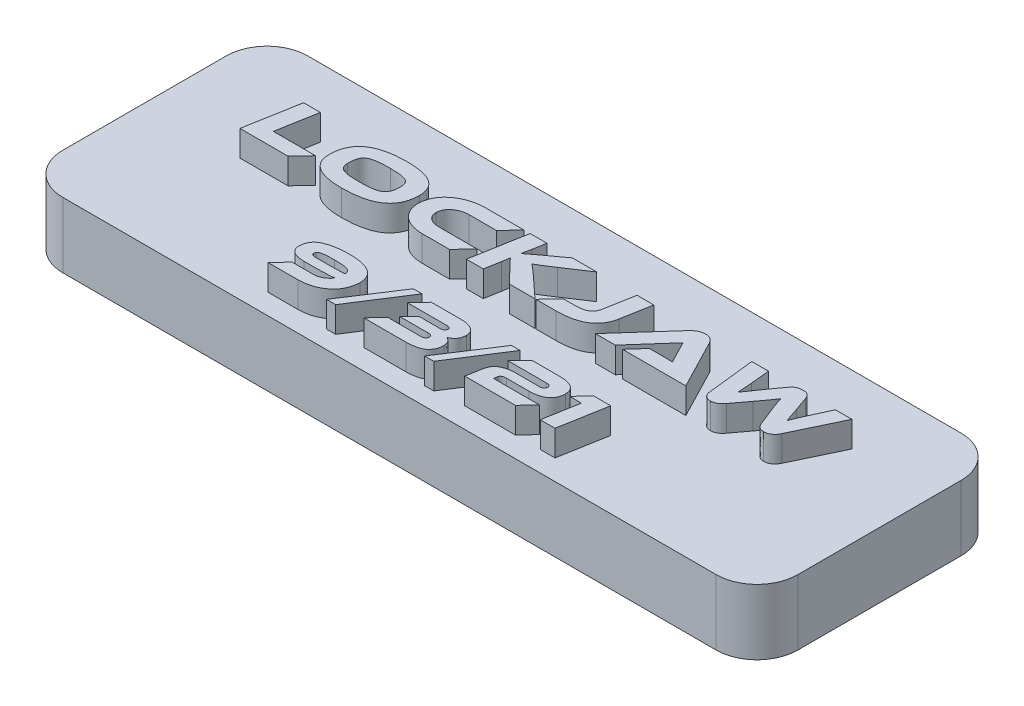
SolidWorks part; units mm, degrees
ref_plane "Front Plane" through (0, 0, 0) normal (0, 0, 1) x (1, 0, 0)
ref_plane "Top Plane" through (0, 0, 0) normal (0, 1, 0) x (1, 0, 0)
ref_plane "Right Plane" through (0, 0, 0) normal (1, 0, 0) x (0, 0, -1)
sketch "Sketch1" plane through (0, 0, 0) normal (0, 1, 0) x (1, 0, 0)
  line L1 (-28.575, 9.525) -> (28.575, 9.525)
  line L2 (-28.575, 9.525) -> (-28.575, -9.525)
  line L3 (-28.575, -9.525) -> (28.575, -9.525)
  line L4 (28.575, 9.525) -> (28.575, -9.525)
  line L5 (-28.575, 9.525) -> (28.575, -9.525) construction
  line L6 (-28.575, -9.525) -> (28.575, 9.525) construction
  point P0 (0, 0)
  dimension "D1" = 57.15
  dimension "D2" = 19.05
extrude "Boss-Extrude1" add sketch "Sketch1" along normal up to surface (5.08 mm away)
fillet "Fillet1" radius 3.175 4 edges at (-28.575, 2.54, 9.525) (-28.575, 2.54, -9.525) (28.575, 2.54, 9.525) (28.575, 2.54, -9.525)
sketch "Sketch3" plane through (0, 5.08, 0) normal (0, 1, 0) x (1, 0, 0)
  line L0 (28.575, -7.9375) -> (-28.575, -7.9375) construction
  line L1 (28.575, -6.35) -> (28.575, 6.35) construction
  line L2 (-28.575, 6.35) -> (-28.575, -6.35) construction
  line L3 (28.575, 0) -> (-28.575, 0) construction
  line L5 (-25.4, -9.525) -> (25.4, -9.525) construction
  line L6 (25.4, 9.525) -> (-25.4, 9.525) construction
  text T0 "LOCKJAW" font "Ethnocentric Rg" height in points 16
  text T1 "9/3/21" font "Ethnocentric Rg" height in points 14
  point P8 (-28.575, 0)
  dimension "D1" = 1.5875
extrude "Boss-Extrude2" add sketch "Sketch3" along normal blind 2
sketch "Sketch4" plane through (0, 0, 0) normal (0, -1, 0) x (1, 0, 0)
  line L0 (25.4, 0) -> (-25.4, 0) construction
  circle A0 centre (-25.4, 0) radius 0.9
  circle A1 centre (25.4, 0) radius 0.9
  point P3 (0, 0)
  dimension "D2" = 1.8
  dimension "D1" = 50.8
extrude "Cut-Extrude1" cut sketch "Sketch4" against normal blind 4
